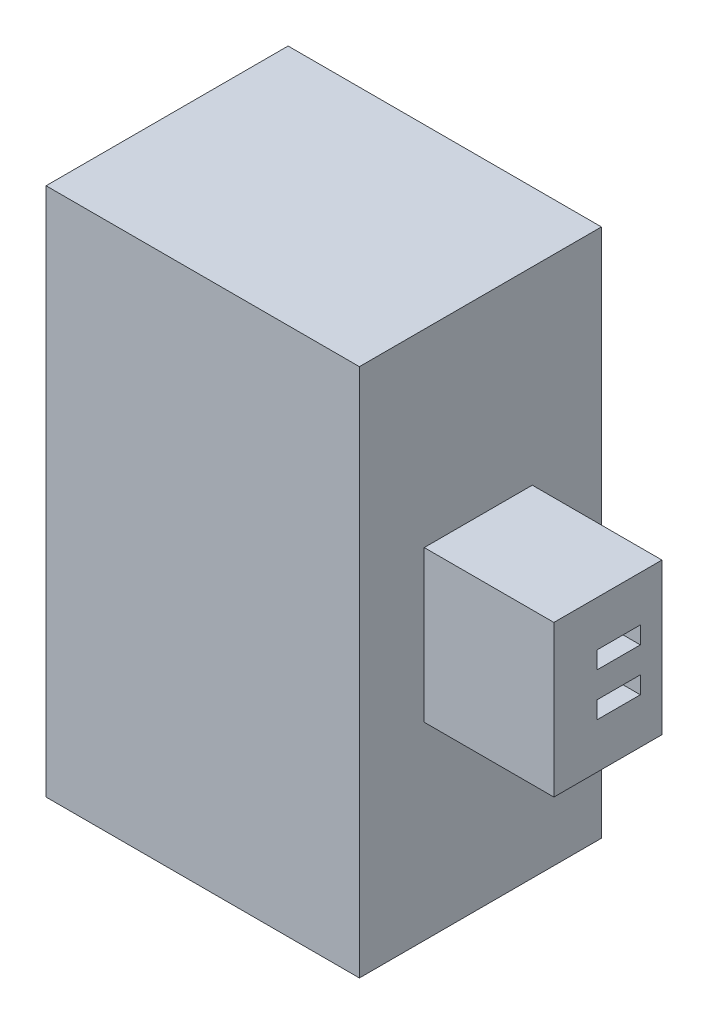
SolidWorks part; units mm, degrees
ref_plane "Front" through (0, 0, 0) normal (0, 0, 1) x (1, 0, 0)
ref_plane "Top" through (0, 0, 0) normal (0, 1, 0) x (1, 0, 0)
ref_plane "Right" through (0, 0, 0) normal (1, 0, 0) x (0, 0, -1)
sketch "Sketch1" plane through (0, 0, 0) normal (0, 0, 1) x (1, 0, 0)
  line L1 (0, 0) -> (5, 0)
  line L2 (0, 0) -> (0, 12.25)
  line L3 (0, 12.25) -> (5, 12.25)
  line L4 (5, 0) -> (5, 12.25)
  dimension "D1" = 12.25
  dimension "D2" = 5
extrude "Boss-Extrude1" add sketch "Sketch1" along normal blind 5.6
sketch "Sketch3" plane through (5, 0, 0) normal (1, 0, 0) x (0, 0, -1)
  line L0 (-1.6, 6.125) -> (0, 6.125) construction
  line L1 (-4.1, 7.875) -> (-1.6, 7.875)
  line L2 (-4.1, 7.875) -> (-4.1, 4.375)
  line L3 (-4.1, 4.375) -> (-1.6, 4.375)
  line L4 (-1.6, 7.875) -> (-1.6, 4.375)
  line L5 (0, 0) -> (0, 12.25) construction
  line L8 (-3.1, 6.625) -> (-2.1, 6.625) construction
  line L9 (-3.1, 6.825) -> (-2.1, 6.825)
  line L10 (-3.1, 6.825) -> (-3.1, 6.425)
  line L11 (-3.1, 6.425) -> (-2.1, 6.425)
  line L12 (-2.1, 6.825) -> (-2.1, 6.425)
  line L13 (-3.1, 5.825) -> (-2.1, 5.825)
  line L14 (-2.1, 5.425) -> (-2.1, 5.825)
  line L15 (-3.1, 5.425) -> (-3.1, 5.825)
  line L16 (-3.1, 5.425) -> (-2.1, 5.425)
  dimension "D1" = 3.5
  dimension "D2" = 2.5
  dimension "D3" = 1
  dimension "D4" = 0.5
  dimension "D5" = 0.4
  dimension "D6" = 1
  dimension "D7" = 1.6
extrude "Boss-Extrude2" add sketch "Sketch3" along normal blind 3
sketch "Sketch4" plane through (0, 0, 0) normal (-1, 0, 0) x (0, 0, 1)
  line L0 (0, 12.25) -> (0, 0) construction
  line L1 (5.6, 12.25) -> (0, 12.25)
  line L2 (5.6, 12.25) -> (5.6, 11.5)
  line L3 (5.6, 11.5) -> (0, 11.5)
  line L4 (0, 12.25) -> (0, 11.5)
  line L5 (5.6, 6.125) -> (0, 6.125) construction
  line L6 (5.6, 12.25) -> (5.6, 0) construction
  line L7 (5.6, 0) -> (5.6, 0.75)
  line L8 (0, 0) -> (0, 0.75)
  line L9 (5.6, 0.75) -> (0, 0.75)
  line L10 (5.6, 0) -> (0, 0)
  dimension "D1" = 0.75
extrude "Boss-Extrude3" add sketch "Sketch4" along normal blind 2.25
sketch "Sketch5" plane through (0, 11.5, 0) normal (0, -1, 0) x (1, 0, 0)
  line L0 (0, 0) -> (0, 5.6) construction
  line L1 (-2.25, 5.6) -> (0, 5.6)
  line L2 (-2.25, 5.6) -> (-2.25, 4.85)
  line L3 (-2.25, 4.85) -> (0, 4.85)
  line L4 (0, 5.6) -> (0, 4.85)
  dimension "D1" = 0.75
extrude "Boss-Extrude4" add sketch "Sketch5" along normal up to surface (10.75 mm away) up to face at (-1.125, 0.75, 2.8)
